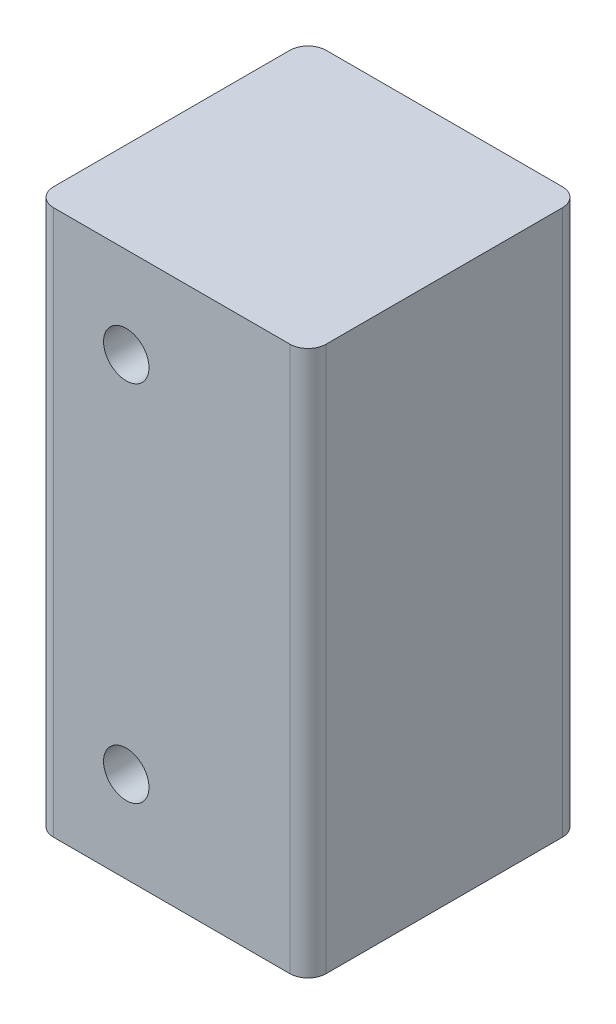
SolidWorks part; units mm, degrees
ref_plane "Plan de face" through (0, 0, 0) normal (0, 0, 1) x (1, 0, 0)
ref_plane "Plan de dessus" through (0, 0, 0) normal (0, 1, 0) x (1, 0, 0)
ref_plane "Plan de droite" through (0, 0, 0) normal (1, 0, 0) x (0, 0, -1)
sketch "Esquisse1" plane through (0, 0, 0) normal (0, 0, 1) x (1, 0, 0)
  line L0 (10, 60) -> (10, 0) construction
  line L1 (0, 0) -> (30, 0)
  line L2 (0, 0) -> (0, 60)
  line L3 (0, 60) -> (30, 60)
  line L4 (30, 0) -> (30, 60)
  line L5 (0, 30) -> (30, 30) construction
  circle A0 centre (10, 50) radius 2.5
  circle A1 centre (10, 10) radius 2.5
  dimension "D3" = 5
  dimension "D1" = 60
  dimension "D2" = 30
  dimension "D4" = 10
  dimension "D5" = 10
extrude "Extrusion1" add sketch "Esquisse1" along normal blind 30
fillet "Congé1" radius 2 4 edges at (0, 30, 0) (30, 30, 0) (30, 30, 30) (0, 30, 30)
